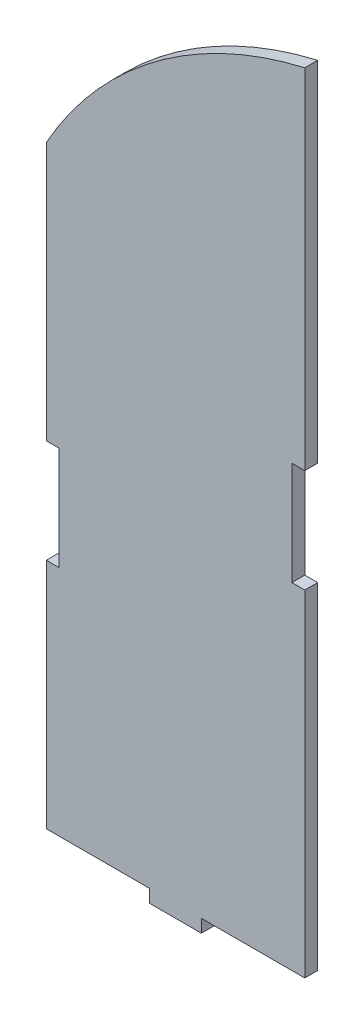
SolidWorks part; units mm, degrees
ref_plane "Plan de face" through (0, 0, 0) normal (0, 0, 1) x (1, 0, 0)
ref_plane "Plan de dessus" through (0, 0, 0) normal (0, 1, 0) x (1, 0, 0)
ref_plane "Plan de droite" through (0, 0, 0) normal (1, 0, 0) x (0, 0, -1)
sketch "Esquisse1" plane through (0, 0, 0) normal (0, 0, 1) x (1, 0, 0)
  line L1 (100, 145.7073) -> (100, 240.7073)
  line L2 (0, 145.7073) -> (0, 235.7073)
  line L3 (100, 315.7073) -> (95, 315.7073)
  line L7 (100, 315.7073) -> (100, 450.7073)
  line L9 (0, 275.7073) -> (5, 275.7073)
  line L10 (5, 275.7073) -> (5, 235.7073)
  line L11 (5, 235.7073) -> (0, 235.7073)
  line L12 (0, 275.7073) -> (0, 375.7073)
  line L13 (0, 145.7073) -> (40, 145.7073)
  line L14 (40, 145.7073) -> (40, 140.7073)
  line L15 (40, 140.7073) -> (60, 140.7073)
  line L16 (60, 140.7073) -> (60, 145.7073)
  line L17 (60, 145.7073) -> (100, 145.7073)
  line L18 (50, 70.7073) -> (50, 182.4992) construction
  line L19 (95, 315.7073) -> (95, 275.7073)
  line L20 (95, 275.7073) -> (100, 275.7073)
  line L21 (100, 275.7073) -> (100, 240.7073)
  arc A0 (0, 375.7073) -> (100, 450.7073) centre (134.7683, 300.1829) cw
  point P5 (2.5, 275.7073)
  dimension "D2" = 310
  dimension "D3" = 5
  dimension "D4" = 230
  dimension "D5" = 135
  dimension "D6" = 40
  dimension "D7" = 5
  dimension "D9" = 40
  dimension "D10" = 135
  dimension "D11" = 5
  dimension "D12" = 50
  dimension "D14" = 10
  dimension "D15" = 10
extrude "Boss.-Extru.1" add sketch "Esquisse1" along normal blind 5
